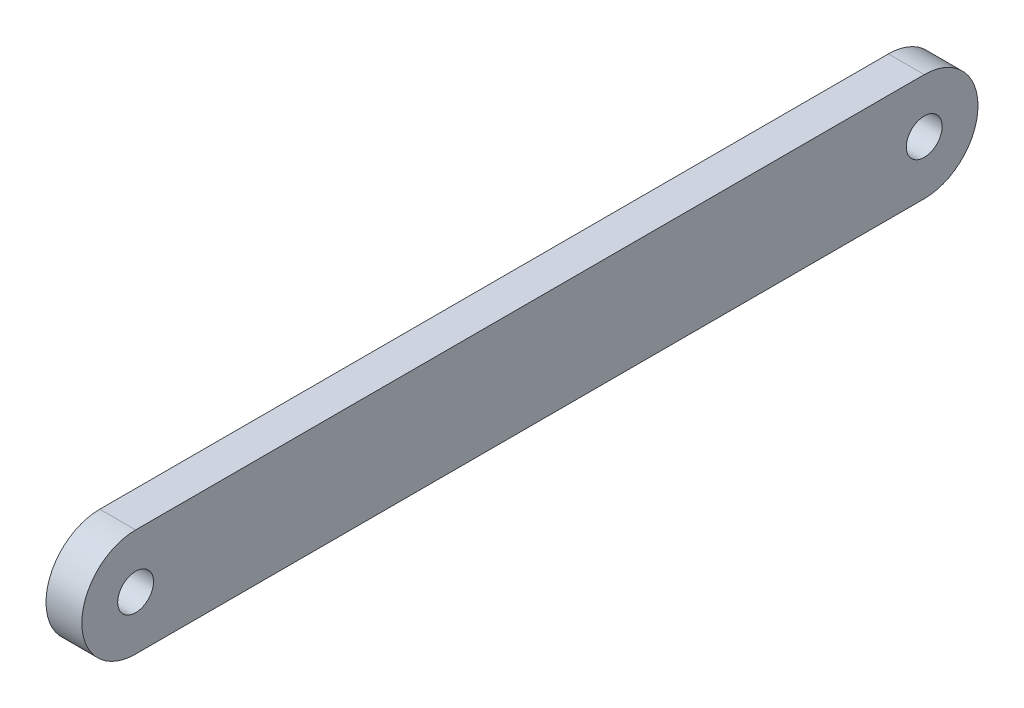
SolidWorks part; units mm, degrees
material "Nylon 101"
ref_plane "Front Plane" through (0, 0, 0) normal (0, 0, 1) x (1, 0, 0)
ref_plane "Top Plane" through (0, 0, 0) normal (0, 1, 0) x (1, 0, 0)
ref_plane "Right Plane" through (0, 0, 0) normal (1, 0, 0) x (0, 0, -1)
sketch "Sketch1" plane through (0, 0, 0) normal (1, 0, 0) x (0, 0, -1)
  line L0 (-110, 0) -> (110, 0) construction
  line L1 (-110, 15) -> (110, 15)
  line L2 (-110, -15) -> (110, -15)
  arc A0 (-110, 15) -> (-110, -15) centre (-110, 0) ccw
  arc A1 (110, -15) -> (110, 15) centre (110, 0) ccw
  point P2 (0, 0)
  dimension "D1" = 15
  dimension "D2" = 220
extrude "Boss-Extrude1" add sketch "Sketch1" along normal blind 10
sketch "Sketch2" plane through (0, 0, 0) normal (-1, 0, 0) x (0, 0, 1)
  circle A0 centre (-110, 0) radius 5
  dimension "D1" = 10
sketch "Sketch3" plane through (0, 0, 0) normal (-1, 0, 0) x (0, 0, 1)
  circle A0 centre (110, 0) radius 5
  dimension "D1" = 10
extrude "Cut-Extrude1" cut sketch "Sketch3" against normal up to next
extrude "Cut-Extrude3" cut sketch "Sketch2" against normal up to next
